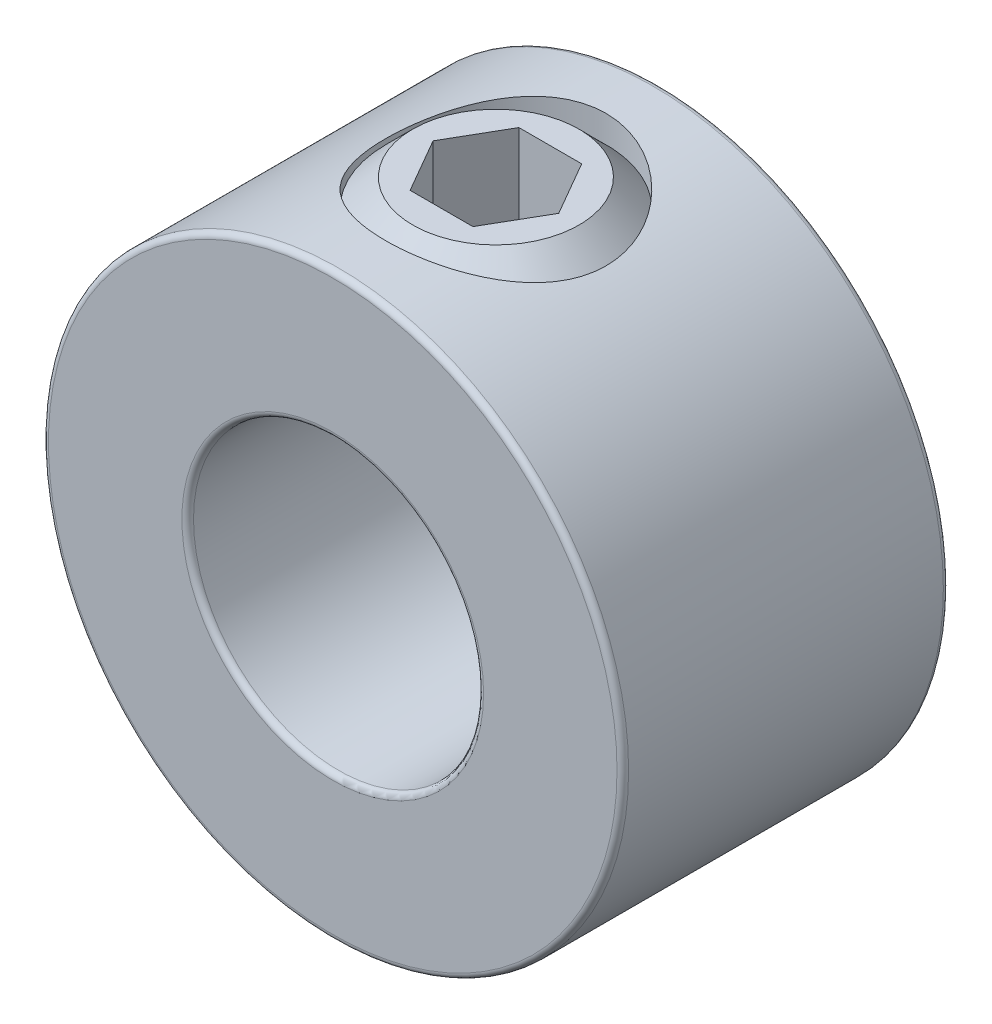
SolidWorks part; units mm, degrees
ref_plane "Front Plane" through (0, 0, 0) normal (0, 0, 1) x (1, 0, 0)
ref_plane "Top Plane" through (0, 0, 0) normal (0, 1, 0) x (1, 0, 0)
ref_plane "Right Plane" through (0, 0, 0) normal (1, 0, 0) x (0, 0, -1)
sketch "Sketch1" plane through (0, 0, 0) normal (0, 0, 1) x (1, 0, 0)
  circle A0 centre (0, 0) radius 6.35
  circle A1 centre (0, 0) radius 3.175
  point P4 (6.35, 0)
  dimension "Bore Dia" = 6.35
  dimension "OD" = 12.7
extrude "Extrude1" add sketch "Sketch1" along normal mid plane 7.1437
sketch "Sketch2" plane through (41.275, 0, 0) normal (0, -1, 0) x (0, 0, -1)
  line L0 (3.5719, -41.275) -> (-3.5719, -41.275) construction
  line L1 (-3.5719, -34.925) -> (-3.5719, -47.625) construction
  line L2 (3.5719, -47.625) -> (3.5719, -34.925) construction
  circle A0 centre (0, -41.275) radius 2.413
  point P7 (0, -43.688)
  dimension "Set Screw Dia" = 4.826
extrude "Cut-Extrude1" cut sketch "Sketch2" against normal through all
fillet "Fillet1" radius 0.127 4 edges at (3.175, 0, -3.5719) (3.175, 0, 3.5719) (6.35, 0, -3.5719) (6.35, 0, 3.5719)
sketch "Sketch3" plane through (0, 0, 0) normal (0, 0, 1) x (1, 0, 0)
  line L0 (-1.8198, 3.175) -> (-0.7119, 3.175)
  line L1 (0, 3.8869) -> (-0.7119, 3.175)
  line L2 (0, 3.8869) -> (0, 6.35)
  line L3 (0, 6.35) -> (-1.8198, 6.35)
  line L4 (-2.413, 3.7682) -> (-2.413, 5.7568)
  line L5 (0, 3.175) -> (0, 0) construction
  line L6 (-2.413, 3.7682) -> (-2.413, 3.175) construction
  line L7 (-2.413, 3.175) -> (-1.8198, 3.175) construction
  line L8 (-2.413, 5.7568) -> (-2.413, 6.35) construction
  line L9 (-1.8198, 3.175) -> (-2.413, 3.7682)
  line L10 (-2.413, 5.7568) -> (-1.8198, 6.35)
  line L11 (-2.413, 6.35) -> (-1.8198, 6.35) construction
  line L12 (-0.7119, 3.175) -> (0, 3.175) construction
  line L13 (0, 3.175) -> (0, 3.8869) construction
  circle A1 centre (0, 0) radius 3.175 construction
  dimension "Screw Length" = 3.175
  dimension "D2" = 0.5932
  dimension "D1" = 0.7119
revolve "Revolve1" add sketch "Sketch3" angle 360 about L5
sketch "Sketch4" plane through (3.3734, 6.35, 0) normal (0, -1, 0) x (0, 0, -1)
  line L1 (0, -1.9986) -> (-1.1906, -2.686)
  line L2 (-1.1906, -2.686) -> (-1.1906, -4.0608)
  line L3 (-1.1906, -4.0608) -> (0, -4.7483)
  line L4 (0, -4.7483) -> (1.1906, -4.0608)
  line L5 (1.1906, -4.0608) -> (1.1906, -2.686)
  line L6 (1.1906, -2.686) -> (0, -1.9986)
  circle A0 centre (0, -3.3734) radius 1.1906 construction
  circle A1 centre (0, -3.3734) radius 1.3748 construction
  dimension "D1" = 2.7496
  dimension "Hex Size" = 2.3813
extrude "Cut-Extrude2" cut sketch "Sketch4" along normal blind 2.3813
equation "\"D1@Fillet1\" = \"OD@Sketch1\"*.01"
equation "\"D1@Cut-Extrude2\" = \"Hex Size@Sketch4\""
equation "\"D2@Sketch3\" =(\"Set Screw Dia@Sketch2\"-\"D1@Sketch4\")/3.5"
equation "\"D1@Sketch3\" = \"D2@Sketch3\"*1.2"
